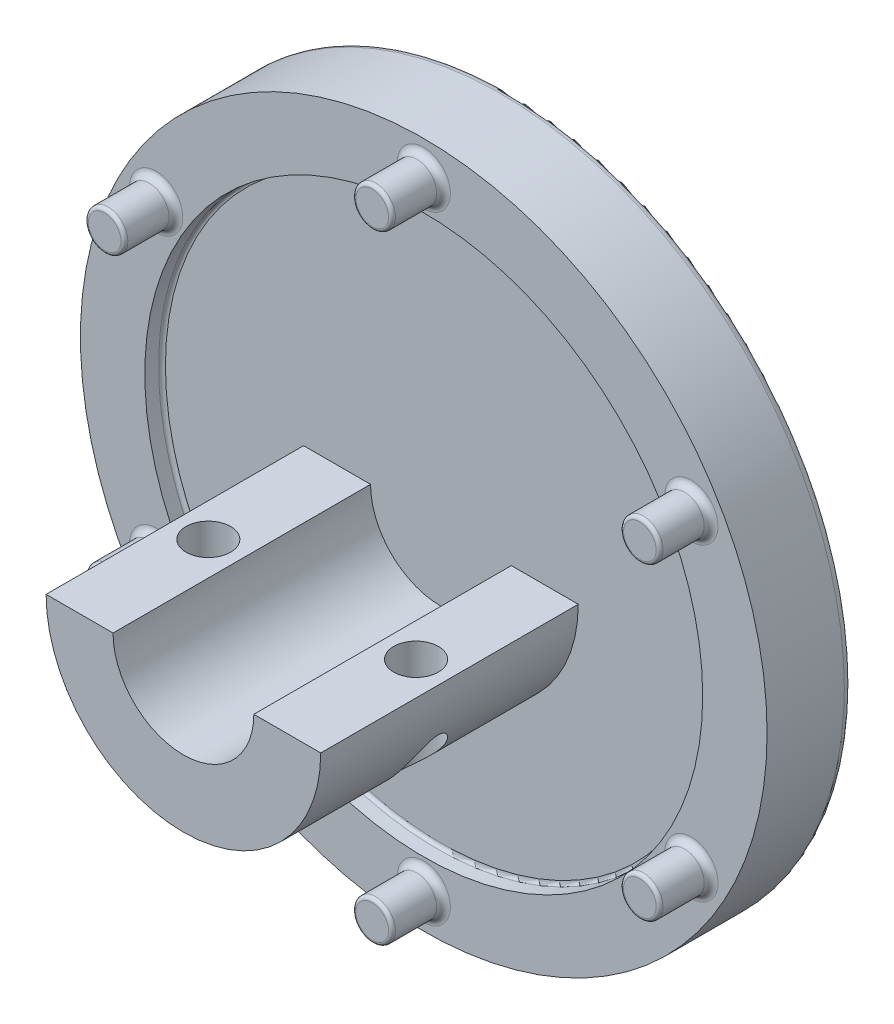
SolidWorks part; units mm, degrees
ref_plane "Front Plane" through (0, 0, 0) normal (0, 0, 1) x (1, 0, 0)
ref_plane "Top Plane" through (0, 0, 0) normal (0, 1, 0) x (1, 0, 0)
ref_plane "Right Plane" through (0, 0, 0) normal (1, 0, 0) x (0, 0, -1)
sketch "Sketch1" plane through (0, 0, 0) normal (0, 0, 1) x (1, 0, 0)
  circle A0 centre (0, 0) radius 20
  dimension "D1" = 40
extrude "Boss-Extrude1" add sketch "Sketch1" along normal blind 5
sketch "Sketch2" plane through (0, 0, 5) normal (0, 0, 1) x (1, 0, 0)
  circle A0 centre (0, 0) radius 18
  dimension "D1" = 36
sketch "Sketch3" plane through (0, 0, 5) normal (0, 0, 1) x (1, 0, 0)
  circle A0 centre (0, 18) radius 1.15
  circle A1 centre (0, 0) radius 18 construction
  circle A2 centre (15.5885, 9) radius 1.15
  circle A3 centre (15.5885, -9) radius 1.15
  circle A4 centre (0, -18) radius 1.15
  circle A5 centre (-15.5885, -9) radius 1.15
  circle A6 centre (-15.5885, 9) radius 1.15
  point P16 (0, 0)
  dimension "D1" = 2.3
  dimension "D2" = 6
extrude "Boss-Extrude3" add sketch "Sketch3" along normal blind 3
fillet "Fillet1" radius 0.4 6 edges at (-14.4385, -9, 5) (1.15, -18, 5) (16.7385, -9, 5) (16.7385, 9, 5) (1.15, 18, 5) (-14.4385, 9, 5)
sketch "Sketch4" plane through (0, 0, 0) normal (0, 0, -1) x (-1, 0, 0)
  circle A0 centre (0, 0) radius 8.5
  dimension "D1" = 17
extrude "Cut-Extrude2" cut sketch "Sketch4" against normal blind 1.5
sketch "Sketch6" plane through (0, 0, 1.5) normal (0, 0, -1) x (-1, 0, 0)
  circle A0 centre (0, 0) radius 5
  dimension "D1" = 10
extrude "Boss-Extrude4" add sketch "Sketch6" along normal blind 0.5
sketch "Sketch7" plane through (0, 0, 1) normal (0, 0, -1) x (-1, 0, 0)
  circle A0 centre (0, 0) radius 3.85
  dimension "D1" = 7.7
extrude "Boss-Extrude6" add sketch "Sketch7" along normal blind 4.5
fillet "Fillet2" radius 0.5 1 edges at (20, 0, 0)
fillet "Fillet3" radius 0.5 1 edges at (-8.5, 0, 0)
fillet "Fillet4" radius 0.5 1 edges at (-3.85, 0, -3.5)
fillet "Fillet5" radius 0.2 6 edges at (1.15, 18, 8) (-14.4385, 9, 8) (-14.4385, -9, 8) (16.7385, -9, 8) (1.15, -18, 8) (16.7385, 9, 8)
sketch "Sketch8" plane through (0, 0, 5) normal (0, 0, 1) x (1, 0, 0)
  circle A0 centre (0, 0) radius 16.25
  dimension "D1" = 32.5
extrude "Cut-Extrude4" cut sketch "Sketch8" against normal blind 1
fillet "Fillet6" radius 0.2 1 edges at (16.25, 0, 4)
sketch "Sketch9" plane through (0, 0, 4) normal (0, 0, 1) x (1, 0, 0)
  line L0 (-4.1, 0) -> (-8, 0)
  line L1 (4.1, 0) -> (8, 0)
  arc A0 (-4.1, 0) -> (4.1, 0) centre (0, 0) ccw
  arc A1 (-8, 0) -> (8, 0) centre (0, 0) ccw
  dimension "D1" = 8.2
  dimension "D2" = 16
extrude "Boss-Extrude7" add sketch "Sketch9" along normal blind 15
sketch "Sketch11" plane through (0, 0, 0) normal (0, 1, 0) x (1, 0, 0)
  circle A0 centre (-6.05, -11.5) radius 1.3
  circle A1 centre (6.05, -11.5) radius 1.3
  dimension "D1" = 2.6
  dimension "D2" = 2.6
extrude "Cut-Extrude5" cut sketch "Sketch11" against normal through all
